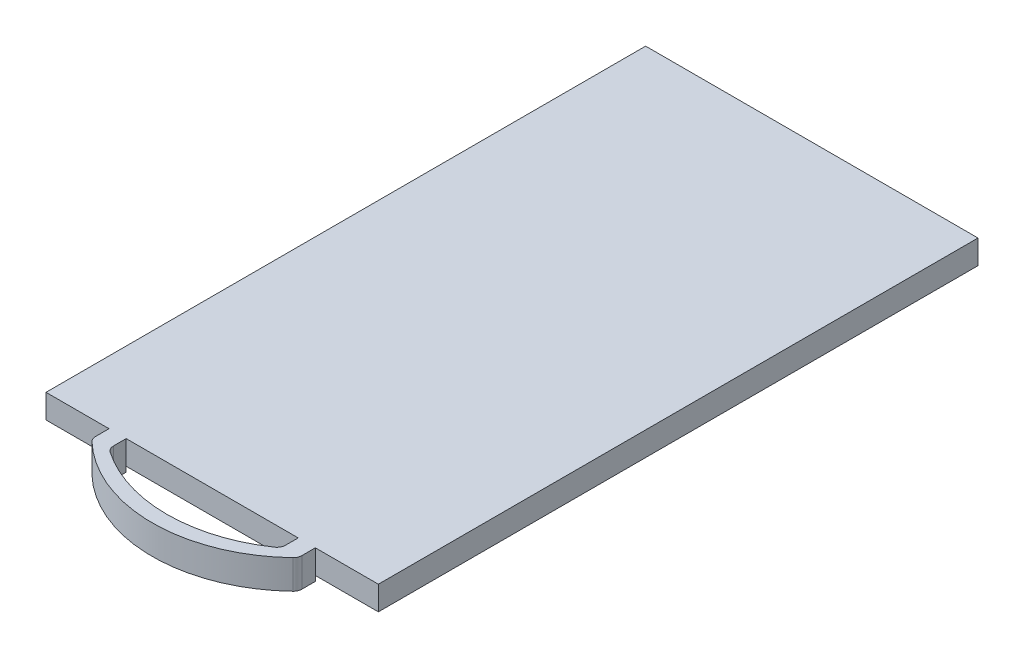
SolidWorks part; units mm, degrees
ref_plane "Alzado" through (0, 0, 0) normal (0, 0, 1) x (1, 0, 0)
ref_plane "Planta" through (0, 0, 0) normal (0, 1, 0) x (1, 0, 0)
ref_plane "Vista lateral" through (0, 0, 0) normal (1, 0, 0) x (0, 0, -1)
sketch "Sketch1" plane through (0, 0, 0) normal (0, 0, 1) x (1, 0, 0)
  line L0 (0, 0) -> (0, 1.4)
  line L1 (0, 1.4) -> (19.4, 1.4)
  line L2 (19.4, 1.4) -> (19.4, 0)
  line L3 (19.4, 0) -> (0, 0)
  dimension "D1" = 19.4
  dimension "D2" = 1.4
extrude "Boss-Extrude1" add sketch "Sketch1" along normal blind 35
sketch "Sketch2" plane through (0, 0, 35) normal (0, 0, 1) x (1, 0, 0)
  line L0 (3.55, 1.4) -> (3.55, 2.4)
  line L1 (19.4, 1.4) -> (0, 1.4) construction
  line L2 (3.55, 2.4) -> (4.05, 2.9)
  line L3 (4.05, 2.9) -> (15.05, 2.9)
  line L4 (15.05, 2.9) -> (15.55, 2.4)
  line L5 (15.55, 2.4) -> (15.55, 1.4)
  line L6 (15.55, 1.4) -> (3.55, 1.4)
  line L7 (19.4, 0) -> (19.4, 1.4) construction
  line L9 (3.55, 2.4) -> (15.55, 2.4) construction
  dimension "D1" = 12
  dimension "D2" = 3.85
  dimension "D3" = 45
  dimension "D4" = 1.5
  dimension "D5" = 1
  dimension "D6" = 1
  dimension "D7" = 45
sketch "Sketch3" plane through (0, 1.4, 0) normal (0, 1, 0) x (1, 0, 0)
  line L0 (3.6792, -35) -> (3.6792, -35.7897)
  line L1 (3.55, -35) -> (15.55, -35) construction
  line L2 (19.4, -35) -> (0, -35) construction
  line L4 (15.7208, -35) -> (15.7208, -35.7897)
  line L5 (3.6792, -35) -> (4.6792, -35)
  line L6 (4.6792, -35) -> (4.6792, -35.7415)
  line L7 (15.7208, -35) -> (14.7208, -35)
  line L8 (14.7208, -35) -> (14.7208, -35.7415)
  arc A0 (3.8342, -36.1516) -> (15.5658, -36.1516) centre (9.7, -30) ccw
  arc A1 (4.8967, -36.154) -> (14.5033, -36.154) centre (9.7, -29.1413) ccw
  arc A2 (15.7208, -35.7897) -> (15.5658, -36.1516) centre (15.2208, -35.7897) cw
  arc A3 (14.7208, -35.7415) -> (14.5033, -36.154) centre (14.2208, -35.7415) cw
  arc A4 (3.6792, -35.7897) -> (3.8342, -36.1516) centre (4.1792, -35.7897) ccw
  arc A5 (4.6792, -35.7415) -> (4.8967, -36.154) centre (5.1792, -35.7415) ccw
  point P14 (9.7, -35)
  point P18 (9.7, -38.5)
  point P19 (15.7208, -36)
  point P22 (14.7208, -36)
  point P25 (3.6792, -36)
  point P28 (4.6792, -36)
  dimension "D3" = 8.5
  dimension "D8" = 8.5
  dimension "D11" = 0.5
  dimension "D1" = 1
  dimension "D2" = 1
  dimension "D4" = 1
  dimension "D5" = 1
  dimension "D6" = 1
  dimension "D7" = 1
  dimension "D10" = 3.5
extrude "Boss-Extrude2" add sketch "Sketch3" against normal blind 1.7
